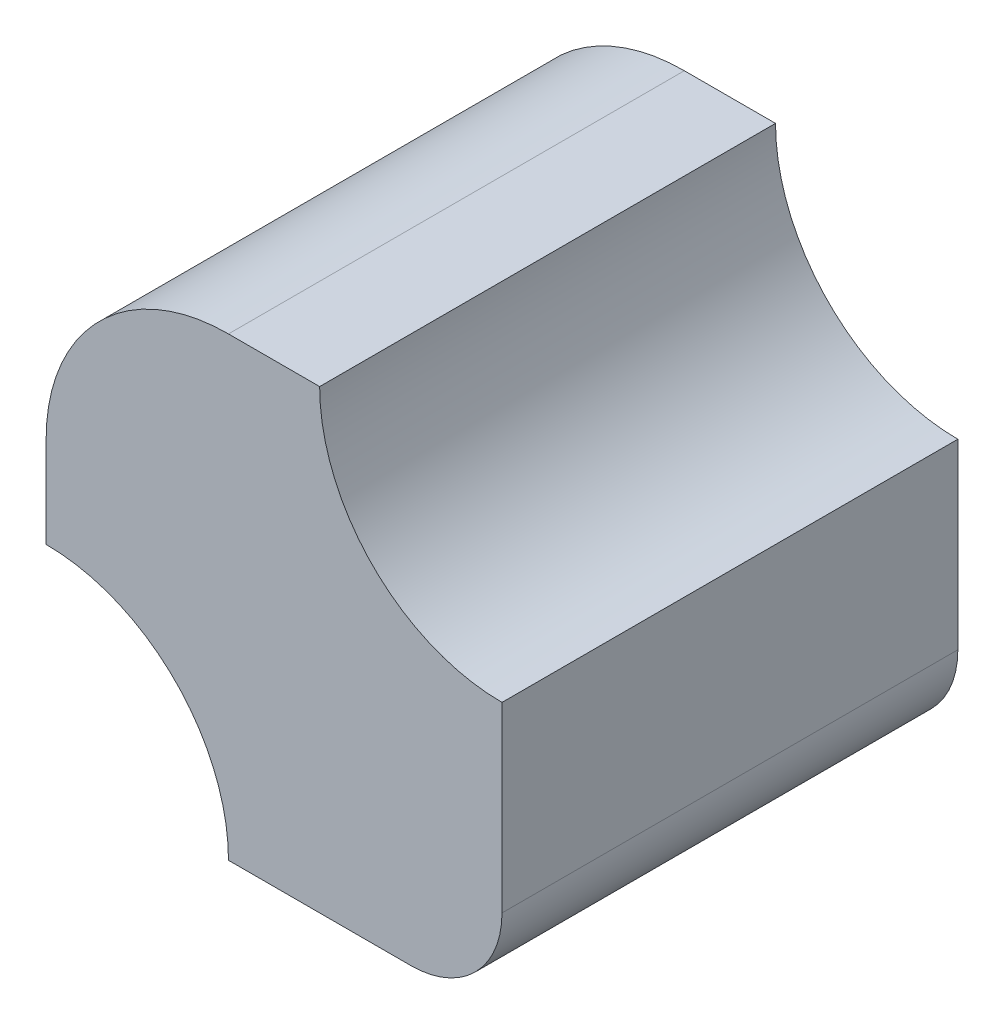
SolidWorks part; units mm, degrees
ref_plane "Front Plane" through (0, 0, 0) normal (0, 0, 1) x (1, 0, 0)
ref_plane "Top Plane" through (0, 0, 0) normal (0, 1, 0) x (1, 0, 0)
ref_plane "Right Plane" through (0, 0, 0) normal (1, 0, 0) x (0, 0, -1)
sketch "Sketch1" plane through (0, 0, 0) normal (0, 0, 1) x (1, 0, 0)
  line L0 (-15, 20) -> (-10, 20)
  line L1 (0, 10) -> (0, 0)
  line L2 (-5, -5) -> (-15, -5)
  line L3 (-25, 5) -> (-25, 10)
  arc A0 (-10, 20) -> (0, 10) centre (0, 20) ccw
  arc A1 (0, 0) -> (-5, -5) centre (-5, 0) cw
  arc A2 (-15, -5) -> (-25, 5) centre (-25, -5) ccw
  arc A3 (-25, 10) -> (-15, 20) centre (-15, 10) cw
  dimension "D5" = 10
  dimension "D6" = 10
  dimension "D7" = 10
  dimension "D1" = 5
  dimension "D2" = 10
  dimension "D3" = 5
  dimension "D4" = 10
extrude "Boss-Extrude1" add sketch "Sketch1" along normal blind 25
